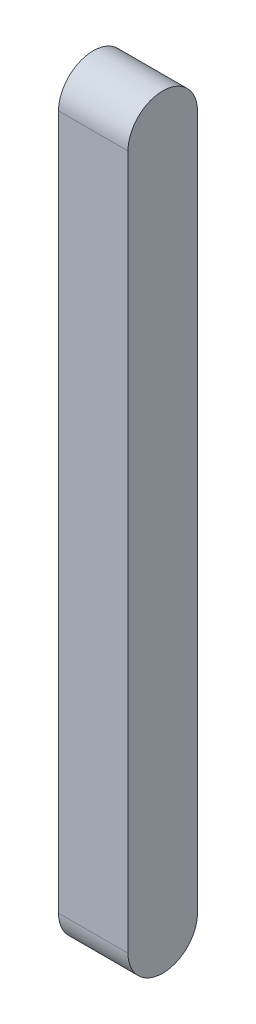
SolidWorks part; units mm, degrees
ref_plane "前视基准面" through (0, 0, 0) normal (0, 0, 1) x (1, 0, 0)
ref_plane "上视基准面" through (0, 0, 0) normal (0, 1, 0) x (1, 0, 0)
ref_plane "右视基准面" through (0, 0, 0) normal (1, 0, 0) x (0, 0, -1)
sketch "草图1" plane through (56.7207, 0, 0) normal (1, 0, 0) x (0, 0, -1)
  line L3 (-45.3961, -21.572) -> (-45.3961, -121.572)
  line L5 (-55.3961, -21.572) -> (-55.3961, -121.572)
  arc A0 (-45.3961, -21.572) -> (-55.3961, -21.572) centre (-50.3961, -21.572) ccw
  arc A1 (-45.3961, -121.572) -> (-55.3961, -121.572) centre (-50.3961, -121.572) cw
  dimension "D1" = 100
  dimension "D2" = 10
extrude "凸台-拉伸1" add sketch "草图1" along normal blind 10
